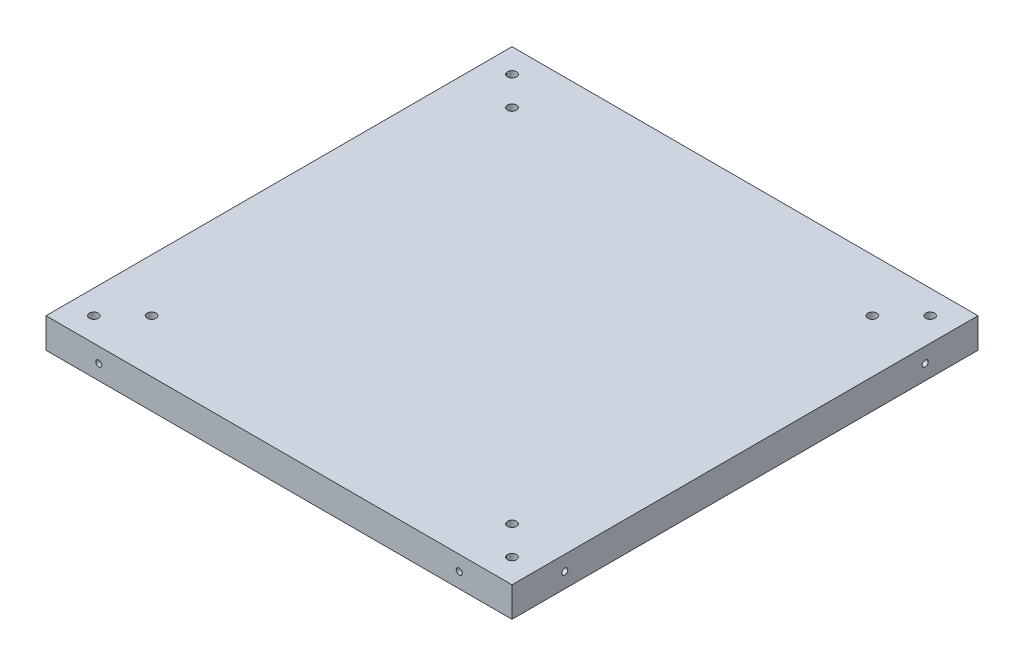
SolidWorks part; units mm, degrees
ref_plane "Front Plane" through (0, 0, 0) normal (0, 0, 1) x (1, 0, 0)
ref_plane "Top Plane" through (0, 0, 0) normal (0, 1, 0) x (1, 0, 0)
ref_plane "Right Plane" through (0, 0, 0) normal (1, 0, 0) x (0, 0, -1)
sketch "Sketch1" plane through (0, 0, 0) normal (0, 1, 0) x (1, 0, 0)
  line L0 (77.4608, -75.0982) -> (77.4608, 74.5774)
  line L1 (74.4472, 77.591) -> (-75.2284, 77.591)
  line L2 (-78.242, 74.5774) -> (-78.242, -75.0982)
  line L3 (-75.2284, -78.1118) -> (74.4472, -78.1118)
  circle A0 centre (-60.6043, -60.4741) radius 1.5
  circle A1 centre (-60.6043, 59.9534) radius 1.5
  circle A2 centre (59.8232, 59.9534) radius 1.5
  circle A3 centre (59.8232, -60.4741) radius 1.5
  arc A4 (77.4608, 74.5774) -> (74.4472, 77.591) centre (74.4472, 74.5774) ccw
  arc A5 (-75.2284, 77.591) -> (-78.242, 74.5774) centre (-75.2284, 74.5774) ccw
  arc A6 (-78.242, -75.0982) -> (-75.2284, -78.1118) centre (-75.2284, -75.0982) ccw
  arc A7 (74.4472, -78.1118) -> (77.4608, -75.0982) centre (74.4472, -75.0982) ccw
  circle A8 centre (0, 0) radius 73
  dimension "D2" = 146
  dimension "D3" = 3
  dimension "D1" = 155.7028
extrude "Boss-Extrude1" add sketch "Sketch1" along normal blind 20
sketch "Sketch4" plane through (0, 20, 0) normal (0, 1, 0) x (1, 0, 0)
  circle A2 centre (0, 0) radius 52.25
  circle A3 centre (0, 0) radius 73 construction
  circle A4 centre (0, 0) radius 73
extrude "Boss-Extrude2" add sketch "Sketch4" against normal blind 10
sketch "Sketch5" plane through (0, 10, 0) normal (0, -1, 0) x (1, 0, 0)
  circle A1 centre (0, 0) radius 73
  circle A2 centre (0, 0) radius 73
  dimension "D1" = 0
extrude "Boss-Extrude3" add sketch "Sketch5" along normal up to surface (10 mm away) up to face at (-0.3906, 0, 0.2604)
sketch "Sketch6" plane through (0, 20, 0) normal (0, 1, 0) x (1, 0, 0)
  line L4 (77.4608, -75.0982) -> (77.4608, 74.5774)
  line L5 (74.4472, 77.591) -> (-75.2284, 77.591)
  line L6 (-78.242, 74.5774) -> (-78.242, -75.0982)
  line L7 (-75.2284, -78.1118) -> (74.4472, -78.1118)
  line L8 (77.4608, -75.0982) -> (77.4608, 74.5774)
  line L9 (74.4472, 77.591) -> (-75.2284, 77.591)
  line L10 (-78.242, 74.5774) -> (-78.242, -75.0982)
  line L11 (-75.2284, -78.1118) -> (74.4472, -78.1118)
  arc A4 (74.4472, -78.1118) -> (77.4608, -75.0982) centre (74.4472, -75.0982) ccw
  arc A5 (77.4608, 74.5774) -> (74.4472, 77.591) centre (74.4472, 74.5774) ccw
  arc A6 (-75.2284, 77.591) -> (-78.242, 74.5774) centre (-75.2284, 74.5774) ccw
  arc A7 (-78.242, -75.0982) -> (-75.2284, -78.1118) centre (-75.2284, -75.0982) ccw
  arc A8 (74.4472, -78.1118) -> (77.4608, -75.0982) centre (74.4472, -75.0982) ccw
  arc A9 (77.4608, 74.5774) -> (74.4472, 77.591) centre (74.4472, 74.5774) ccw
  arc A10 (-75.2284, 77.591) -> (-78.242, 74.5774) centre (-75.2284, 74.5774) ccw
  arc A11 (-78.242, -75.0982) -> (-75.2284, -78.1118) centre (-75.2284, -75.0982) ccw
  dimension "D1" = 0
extrude "Cut-Extrude1" cut sketch "Sketch6" against normal up to surface (10 mm away) up to face at (0, 10, 52.25)
sketch "Sketch7" plane through (0, 10, 0) normal (0, 1, 0) x (1, 0, 0)
  line L0 (-0.3906, 77.591) -> (-0.3906, -78.1118) construction
  line L1 (74.4472, 77.591) -> (-75.2284, 77.591) construction
  line L2 (-75.2284, -78.1118) -> (74.4472, -78.1118) construction
  line L4 (77.4608, 77.591) -> (-78.242, 77.591)
  line L5 (77.4608, 77.591) -> (77.4608, -78.1118)
  line L6 (77.4608, -78.1118) -> (-78.242, -78.1118)
  line L7 (-78.242, 77.591) -> (-78.242, -78.1118)
  line L8 (-0.3906, -78.1118) -> (-0.3906, 77.591) construction
  line L9 (77.4608, -0.2604) -> (-78.242, -0.2604) construction
  circle A0 centre (59.8232, 59.9534) radius 1.5 construction
  circle A1 centre (59.8232, -60.4741) radius 1.5 construction
  circle A2 centre (-60.6043, -60.4741) radius 1.5 construction
  circle A3 centre (-60.6043, 59.9534) radius 1.5 construction
  circle A4 centre (59.8232, 59.9534) radius 1.5
  circle A5 centre (59.8232, -60.4741) radius 1.5
  circle A6 centre (-60.6043, -60.4741) radius 1.5
  circle A7 centre (-60.6043, 59.9534) radius 1.5
  point P6 (-0.3906, -0.2604)
extrude "Boss-Extrude4" add sketch "Sketch7" against normal blind 10
sketch "Sketch8" plane through (0, 10, 0) normal (0, 1, 0) x (1, 0, 0)
  line L0 (-70.242, 77.591) -> (-70.242, 69.591) construction
  line L3 (77.4608, 77.591) -> (-78.242, 77.591) construction
  line L5 (-78.242, 69.591) -> (-70.242, 69.591) construction
  line L7 (-78.242, 77.591) -> (-78.242, -78.1118) construction
  line L8 (-0.3906, 77.591) -> (-0.3906, -78.1118) construction
  line L9 (-78.242, -78.1118) -> (77.4608, -78.1118) construction
  line L10 (-78.242, -0.2604) -> (77.4608, -0.2604) construction
  line L11 (77.4608, -78.1118) -> (77.4608, 77.591) construction
  line L12 (77.4608, 69.591) -> (69.4608, 69.591) construction
  line L13 (69.4608, 77.591) -> (69.4608, 69.591) construction
  line L14 (69.4608, -78.1118) -> (69.4608, -70.1118) construction
  line L15 (77.4608, -70.1118) -> (69.4608, -70.1118) construction
  line L16 (-78.242, -70.1118) -> (-70.242, -70.1118) construction
  line L17 (-70.242, -78.1118) -> (-70.242, -70.1118) construction
  circle A4 centre (-70.242, 69.591) radius 1.5
  circle A5 centre (69.4608, 69.591) radius 1.5
  circle A6 centre (69.4608, -70.1118) radius 1.5
  circle A7 centre (-70.242, -70.1118) radius 1.5
  dimension "D1" = 8
  dimension "D3" = 3
  dimension "D2" = 8
extrude "Cut-Extrude2" cut sketch "Sketch8" against normal blind 58
sketch "Sketch9" plane through (0, 10, 0) normal (0, 1, 0) x (1, 0, 0)
  circle A0 centre (-60.6043, 59.9534) radius 3
  circle A1 centre (59.8232, 59.9534) radius 3
  circle A2 centre (59.8232, -60.4741) radius 3
  circle A3 centre (-60.6043, -60.4741) radius 3
  dimension "D1" = 6
  dimension "D2" = 6
extrude "Cut-Extrude3" cut sketch "Sketch9" against normal blind 3
sketch "Sketch10" plane through (0, 0, 0) normal (0, -1, 0) x (1, 0, 0)
  circle A0 centre (59.8232, -59.9534) radius 3 construction
  circle A1 centre (-60.6043, -59.9534) radius 3 construction
  circle A2 centre (-60.6043, 60.4741) radius 3 construction
  circle A3 centre (59.8232, 60.4741) radius 3 construction
  circle A4 centre (59.8232, -59.9534) radius 3
  circle A5 centre (-60.6043, -59.9534) radius 3
  circle A6 centre (-60.6043, 60.4741) radius 3
  circle A7 centre (59.8232, 60.4741) radius 3
extrude "Cut-Extrude4" cut sketch "Sketch10" against normal blind 3
sketch "Sketch11" plane through (0, 10, 0) normal (0, 1, 0) x (1, 0, 0)
  circle A0 centre (-60.6043, -60.4741) radius 3 construction
  circle A1 centre (59.8232, -60.4741) radius 3 construction
  circle A2 centre (59.8232, 59.9534) radius 3 construction
  circle A3 centre (-60.6043, 59.9534) radius 3 construction
  circle A4 centre (-60.6043, -60.4741) radius 3
  circle A5 centre (59.8232, -60.4741) radius 3
  circle A6 centre (59.8232, 59.9534) radius 3
  circle A7 centre (-60.6043, 59.9534) radius 3
  circle A8 centre (-60.6043, 59.9534) radius 1.5 construction
  circle A9 centre (-60.6043, -60.4741) radius 1.5 construction
  circle A10 centre (59.8232, -60.4741) radius 1.5 construction
  circle A11 centre (59.8232, 59.9534) radius 1.5 construction
  circle A12 centre (-60.6043, -60.4741) radius 1.5
  circle A13 centre (59.8232, -60.4741) radius 1.5
  circle A14 centre (59.8232, 59.9534) radius 1.5
  circle A15 centre (-60.6043, 59.9534) radius 1.5
extrude "Boss-Extrude6" add sketch "Sketch11" against normal blind 3
sketch "Sketch13" plane through (0, 0, -77.591) normal (0, 0, -1) x (-1, 0, 0)
  line L0 (-77.4608, 0) -> (78.242, 0) construction
  line L1 (-77.4608, 0) -> (78.242, 0)
  line L2 (-77.4608, 0) -> (78.242, 0)
  circle A0 centre (-59.8232, 5) radius 1
  circle A1 centre (60.6043, 5) radius 1
  point P2 (0.3906, 0)
  point P9 (0.3906, 0)
extrude "Cut-Extrude6" cut sketch "Sketch13" against normal blind 5 contours A0 | A1
sketch "Sketch14" plane through (-78.242, 0, 0) normal (-1, 0, 0) x (0, 0, 1)
  line L0 (-77.591, 0) -> (78.1118, 0) construction
  line L1 (-77.591, 0) -> (78.1118, 0)
  circle A0 centre (-59.9534, 5) radius 1
  circle A1 centre (60.4741, 5) radius 1
  point P0 (0.2604, 0)
extrude "Cut-Extrude7" cut sketch "Sketch14" against normal blind 5 contours A0 | A1
sketch "Sketch15" plane through (0, 0, 78.1118) normal (0, 0, 1) x (1, 0, 0)
  circle A0 centre (-60.6043, 5) radius 1 construction
  circle A1 centre (59.8232, 5) radius 1 construction
  circle A2 centre (-60.6043, 5) radius 1
  circle A3 centre (59.8232, 5) radius 1
extrude "Cut-Extrude8" cut sketch "Sketch15" against normal blind 5
sketch "Sketch16" plane through (77.4608, 0, 0) normal (1, 0, 0) x (0, 0, -1)
  circle A0 centre (59.9534, 5) radius 1 construction
  circle A1 centre (-60.4741, 5) radius 1 construction
  circle A2 centre (59.9534, 5) radius 1
  circle A3 centre (-60.4741, 5) radius 1
extrude "Cut-Extrude9" cut sketch "Sketch16" against normal blind 5
